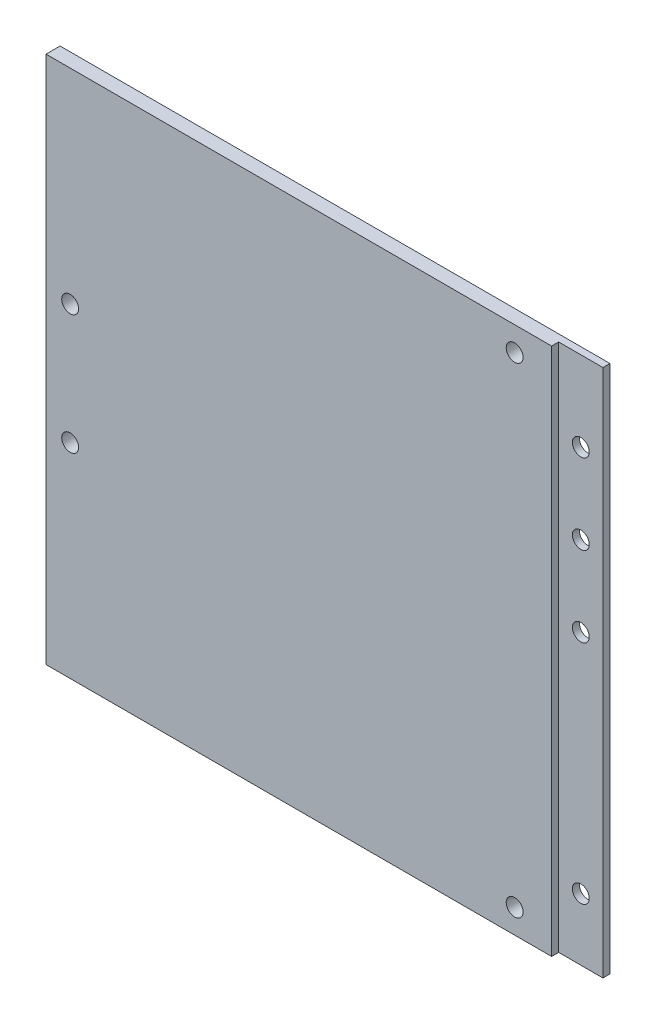
SolidWorks part; units mm, degrees
ref_plane "Front Plane" through (0, 0, 0) normal (0, 0, 1) x (1, 0, 0)
ref_plane "Top Plane" through (0, 0, 0) normal (0, 1, 0) x (1, 0, 0)
ref_plane "Right Plane" through (0, 0, 0) normal (1, 0, 0) x (0, 0, -1)
sketch "Sketch2" plane through (0, 0, 0) normal (0, 0, 1) x (1, 0, 0)
  line L1 (-21.3193, 8.8196) -> (102.8537, 8.8196)
  line L2 (-21.3193, 8.8196) -> (-21.3193, -110.5604)
  line L3 (-21.3193, -110.5604) -> (102.8537, -110.5604)
  line L4 (102.8537, 8.8196) -> (102.8537, -110.5604)
  dimension "D1" = 124.173
  dimension "D2" = 119.38
extrude "Boss-Extrude1" add sketch "Sketch2" along normal blind 3.175
sketch "Sketch4" plane through (0, 0, 0) normal (0, 0, 1) x (1, 0, 0)
  line L0 (102.8537, -110.5604) -> (102.8537, 8.8196) construction
  line L10 (-21.3193, -110.5604) -> (102.8537, -110.5604) construction
  circle A0 centre (-15.8673, -37.3204) radius 1.905
  circle A1 centre (-15.8673, -64.4224) radius 1.905
  circle A2 centre (84.5037, 3.3676) radius 1.905
  circle A3 centre (84.5037, -105.1084) radius 1.905
  dimension "D1" = 18.35
  dimension "D2" = 18.35
  dimension "D6" = 27.102
  dimension "D8" = 5.452
extrude "Cut-Extrude1" cut sketch "Sketch4" along normal blind 14.175
sketch "Sketch10" plane through (102.8537, 0, 0) normal (1, 0, 0) x (0, 0, -1)
  line L1 (-3.175, 8.8196) -> (-1.585, 8.8196)
  line L2 (-3.175, 8.8196) -> (-3.175, -111.1804)
  line L3 (-3.175, -111.1804) -> (-1.585, -111.1804)
  line L4 (-1.585, 8.8196) -> (-1.585, -111.1804)
  dimension "D1" = 1.59
  dimension "D2" = 120
extrude "Cut-Extrude3" cut sketch "Sketch10" against normal blind 10
sketch "Sketch11" plane through (0, 0, 1.585) normal (0, 0, 1) x (1, 0, 0)
  line L0 (102.8537, -110.5604) -> (92.8537, -110.5604) construction
  line L1 (92.8537, 8.8196) -> (102.8537, 8.8196) construction
  line L2 (102.8537, -110.5604) -> (102.8537, 8.8196) construction
  circle A0 centre (97.8537, -9.2604) radius 1.905
  circle A1 centre (97.8537, -27.3504) radius 1.905
  circle A2 centre (97.8537, -45.4304) radius 1.905
  circle A3 centre (97.8537, -96.5604) radius 1.905
  dimension "D1" = 14
  dimension "D2" = 18.08
  dimension "D3" = 5
  dimension "D4" = 5
  dimension "D5" = 5
  dimension "D6" = 18.09
  dimension "D7" = 18.08
  dimension "D8" = 5
extrude "Cut-Extrude4" cut sketch "Sketch11" against normal blind 10
